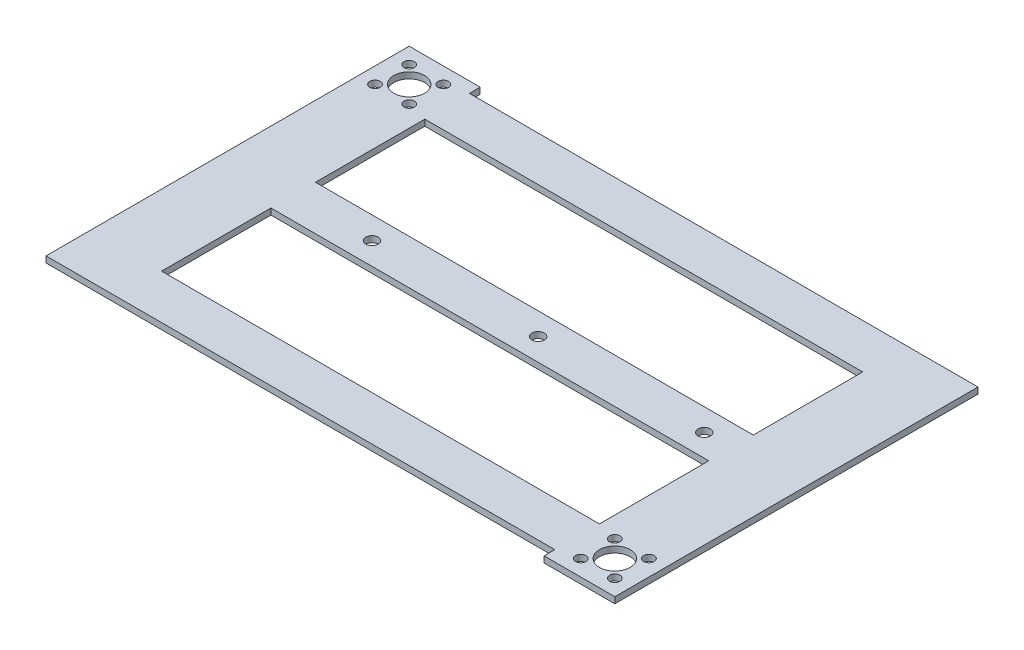
SolidWorks part; units mm, degrees
ref_plane "Front Plane" through (0, 0, 0) normal (0, 0, 1) x (1, 0, 0)
ref_plane "Top Plane" through (0, 0, 0) normal (0, 1, 0) x (1, 0, 0)
ref_plane "Right Plane" through (0, 0, 0) normal (1, 0, 0) x (0, 0, -1)
sketch "Sketch1" plane through (0, 0, 0) normal (0, 1, 0) x (1, 0, 0)
  line L0 (-95.0509, 92.8338) -> (57.8211, 92.8338) construction
  line L1 (-91.977, 142.8838) -> (-86.977, 142.8838) construction
  line L2 (-86.977, 142.8838) -> (-91.977, 142.8838) construction
  line L3 (67.7305, 150.1338) -> (82.2305, 150.1338)
  line L4 (-99.227, 35.5316) -> (-84.727, 35.5316)
  line L5 (-84.727, 35.5316) -> (62.7305, 35.5316)
  line L6 (-79.6432, 50.0316) -> (62.7305, 50.0316)
  line L7 (-79.6432, 150.1338) -> (67.7305, 150.1338)
  line L8 (-79.6432, 135.6338) -> (62.7305, 135.6338)
  line L9 (-79.6432, 100.0827) -> (62.7305, 100.0827)
  line L10 (-79.6432, 85.5827) -> (62.7305, 85.5827)
  line L17 (-84.6432, 153.6338) -> (-79.6432, 153.6338)
  line L18 (-84.6432, 153.6338) -> (-102.727, 153.6338)
  line L19 (-102.727, 100.0827) -> (-102.727, 153.6338)
  line L20 (-79.6432, 153.4321) -> (-79.6432, 150.1338)
  line L21 (-79.6432, 135.6338) -> (-79.6432, 100.0827)
  line L22 (-79.6432, 85.5827) -> (-79.6432, 50.0316)
  line L23 (-102.727, 85.5827) -> (-102.727, 35.5316)
  line L24 (-102.727, 35.5316) -> (-99.227, 35.5316)
  line L25 (67.7305, 32.0316) -> (62.7305, 32.0316)
  line L26 (67.7305, 32.0316) -> (85.7305, 32.0316)
  line L27 (85.7305, 50.0316) -> (85.7305, 32.0316)
  line L28 (62.7305, 32.0316) -> (62.7305, 35.5316)
  line L29 (62.7305, 50.0316) -> (62.7305, 85.5827)
  line L30 (62.7305, 100.0827) -> (62.7305, 135.6338)
  line L31 (85.7305, 50.0316) -> (85.7305, 85.5827)
  line L32 (85.7305, 100.0827) -> (85.7305, 150.1338)
  line L33 (85.7305, 150.1338) -> (82.2305, 150.1338)
  line L34 (-79.6432, 153.4321) -> (-79.6432, 153.6338)
  line L35 (0, -55) -> (0, 55) construction
  line L36 (-102.727, 100.0827) -> (-102.727, 98.9236)
  line L37 (85.7305, 100.0827) -> (85.7305, 85.5827)
  line L41 (-102.727, 92.8327) -> (-102.727, 85.5827)
  line L42 (-102.727, 98.9236) -> (-102.727, 92.8327)
  circle A0 centre (-91.977, 142.8838) radius 5
  circle A1 centre (74.9805, 42.7816) radius 5
  circle A2 centre (-86.427, 148.4338) radius 1.7
  circle A3 centre (-97.527, 148.4338) radius 1.7
  circle A4 centre (-86.427, 137.3338) radius 1.7
  circle A5 centre (-97.527, 137.3338) radius 1.7
  circle A6 centre (69.4305, 48.3316) radius 1.7
  circle A7 centre (80.5305, 48.3316) radius 1.7
  circle A8 centre (80.5305, 37.2316) radius 1.7
  circle A9 centre (69.4305, 37.2316) radius 1.7
  circle A10 centre (-54, 92.8338) radius 2
  circle A11 centre (0, 92.8338) radius 2
  circle A13 centre (54, 92.8338) radius 2
  dimension "D1" = 3.4
  dimension "D2" = 3.4
  dimension "D5" = 4
  dimension "D6" = 4
  dimension "D7" = 4
  dimension "D8" = 54
  dimension "D3" = 5
  dimension "D4" = 5
  dimension "D9" = 54
  dimension "D10" = 0
extrude "Boss-Extrude1" add sketch "Sketch1" along normal blind 2
